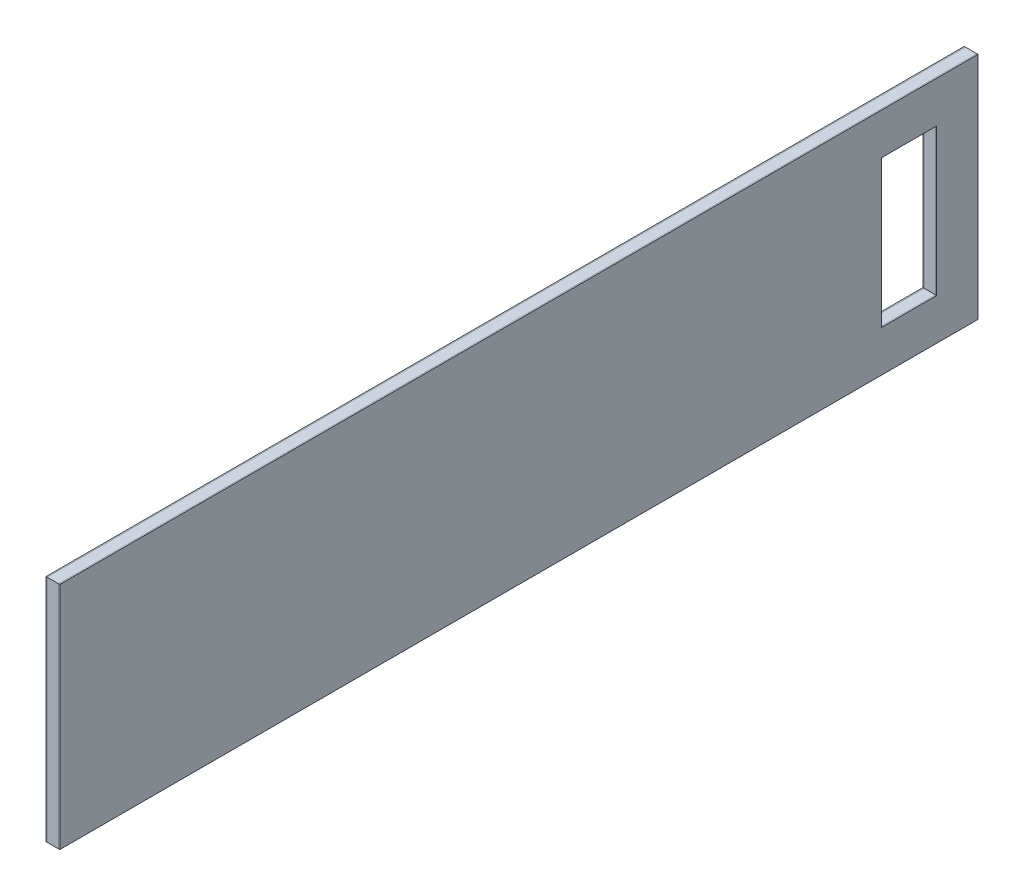
SolidWorks part; units mm, degrees
ref_plane "Front Plane" through (0, 0, 0) normal (0, 0, 1) x (1, 0, 0)
ref_plane "Top Plane" through (0, 0, 0) normal (0, 1, 0) x (1, 0, 0)
ref_plane "Right Plane" through (0, 0, 0) normal (1, 0, 0) x (0, 0, -1)
sketch "Sketch1" plane through (0, 0, 0) normal (1, 0, 0) x (0, 0, -1)
  line L1 (-100, 25) -> (100, 25)
  line L2 (-100, 25) -> (-100, -25)
  line L3 (-100, -25) -> (100, -25)
  line L4 (100, 25) -> (100, -25)
  line L7 (79, 16) -> (91, 16)
  line L8 (79, 16) -> (79, -16)
  line L9 (79, -16) -> (91, -16)
  line L10 (91, 16) -> (91, -16)
  point P0 (0, 0)
  point P6 (85, 0)
  dimension "D1" = 200
  dimension "D2" = 50
  dimension "D3" = 9
  dimension "D4" = 9
  dimension "D5" = 12
extrude "Boss-Extrude1" add sketch "Sketch1" along normal blind 0.25
sketch "Sketch2" plane through (0, 0, 0) normal (-1, 0, 0) x (0, 0, 1)
  line L4 (-91, 16) -> (-91, -16)
  line L5 (-79, 16) -> (-91, 16)
  line L6 (-79, -16) -> (-79, 16)
  line L7 (-91, -16) -> (-79, -16)
  line L8 (-91, 16) -> (-91, -16)
  line L9 (-79, 16) -> (-91, 16)
  line L10 (-79, -16) -> (-79, 16)
  line L11 (-91, -16) -> (-79, -16)
  line M5 (-100, 25) -> (-100, -25)
  line M6 (-100, -25) -> (100, -25)
  line M7 (100, -25) -> (100, 25)
  line M8 (100, 25) -> (-100, 25)
  line M9 (-91, -16) -> (-91, 16)
  line M10 (-91, 16) -> (-79, 16)
  line M11 (-79, 16) -> (-79, -16)
  line M12 (-79, -16) -> (-91, -16)
  dimension "D1" = 0
extrude "Boss-Extrude2" add sketch "Sketch2" along normal blind 2.5 separate body contours M8 M5 M6 M7 M12 M9 M10 M11
sketch "Sketch3" plane through (-2.5, 0, 0) normal (-1, 0, 0) x (0, 0, 1)
  line L4 (-91, -16) -> (-79, -16)
  line L5 (-91, 16) -> (-91, -16)
  line L6 (-79, 16) -> (-91, 16)
  line L7 (-79, -16) -> (-79, 16)
  line L8 (-91, -16) -> (-79, -16)
  line L9 (-91, 16) -> (-91, -16)
  line L10 (-79, 16) -> (-91, 16)
  line L11 (-79, -16) -> (-79, 16)
  line M5 (-79, -16) -> (-91, -16)
  line M6 (-91, -16) -> (-91, 16)
  line M7 (-91, 16) -> (-79, 16)
  line M8 (-79, 16) -> (-79, -16)
  line M9 (100, 25) -> (-100, 25)
  line M10 (-100, 25) -> (-100, -25)
  line M11 (-100, -25) -> (100, -25)
  line M12 (100, -25) -> (100, 25)
  dimension "D1" = 0
extrude "Boss-Extrude3" add sketch "Sketch3" along normal blind 0.25 separate body contours M12 M9 M10 M11 M8 M5 M6 M7
